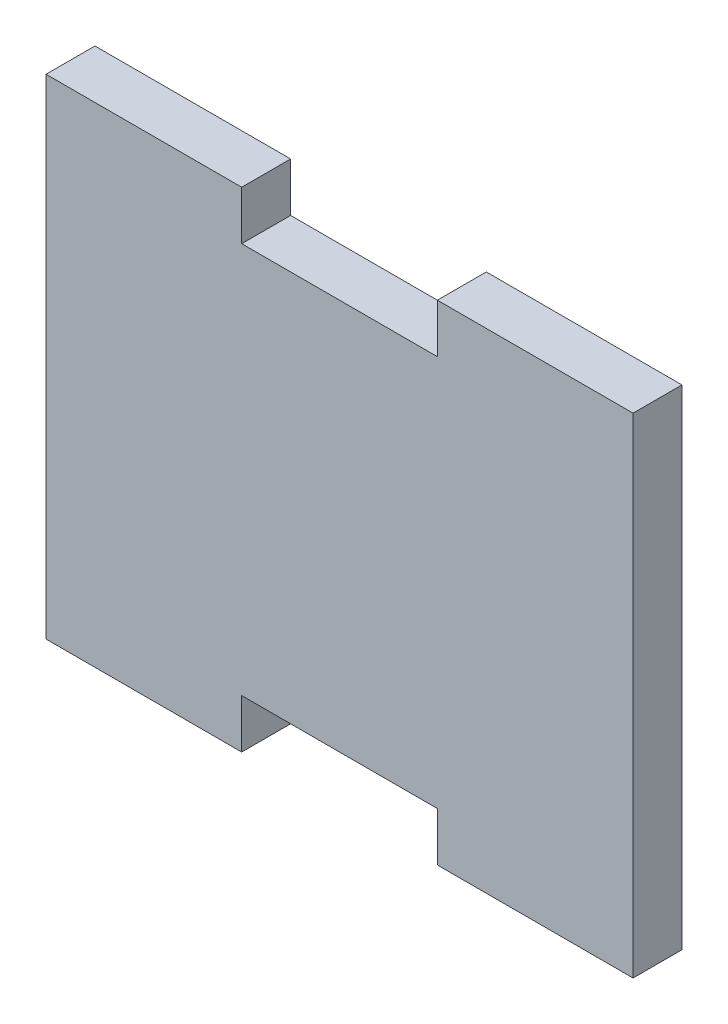
SolidWorks part; units mm, degrees
ref_plane "Front Plane" through (0, 0, 0) normal (0, 0, 1) x (1, 0, 0)
ref_plane "Top Plane" through (0, 0, 0) normal (0, 1, 0) x (1, 0, 0)
ref_plane "Right Plane" through (0, 0, 0) normal (1, 0, 0) x (0, 0, -1)
sketch "Sketch1" plane through (0, 0, 0) normal (0, 0, 1) x (1, 0, 0)
  line L1 (-30, 20) -> (30, 20)
  line L2 (-30, 20) -> (-30, -20)
  line L3 (-30, -20) -> (30, -20)
  line L4 (30, 20) -> (30, -20)
  line L5 (-30, 20) -> (30, -20) construction
  line L6 (-30, -20) -> (30, 20) construction
  line L7 (-30, 20) -> (-10, 20)
  line L8 (-30, 20) -> (-30, 25)
  line L9 (-30, 25) -> (-10, 25)
  line L10 (-10, 20) -> (-10, 25)
  line L11 (30, 20) -> (10, 20)
  line L12 (30, 20) -> (30, 25)
  line L13 (30, 25) -> (10, 25)
  line L14 (10, 20) -> (10, 25)
  line L15 (30, -20) -> (10, -20)
  line L16 (30, -20) -> (30, -25)
  line L17 (30, -25) -> (10, -25)
  line L18 (10, -20) -> (10, -25)
  line L19 (-30, -20) -> (-10, -20)
  line L20 (-30, -20) -> (-30, -25)
  line L21 (-30, -25) -> (-10, -25)
  line L22 (-10, -20) -> (-10, -25)
  point P0 (0, 0)
  dimension "D1" = 60
  dimension "D2" = 40
  dimension "D3" = 20
  dimension "D4" = 20
  dimension "D5" = 5
  dimension "D6" = 5
  dimension "D7" = 20
  dimension "D8" = 20
  dimension "D9" = 5
  dimension "D10" = 5
extrude "Boss-Extrude1" add sketch "Sketch1" along normal blind 5 contours L4 L1 L2 L3 | L1 L10 L9 L8 | L3 L18 L17 L16 | L22 L3 L20 L21 | L12 L13 L14 L11
